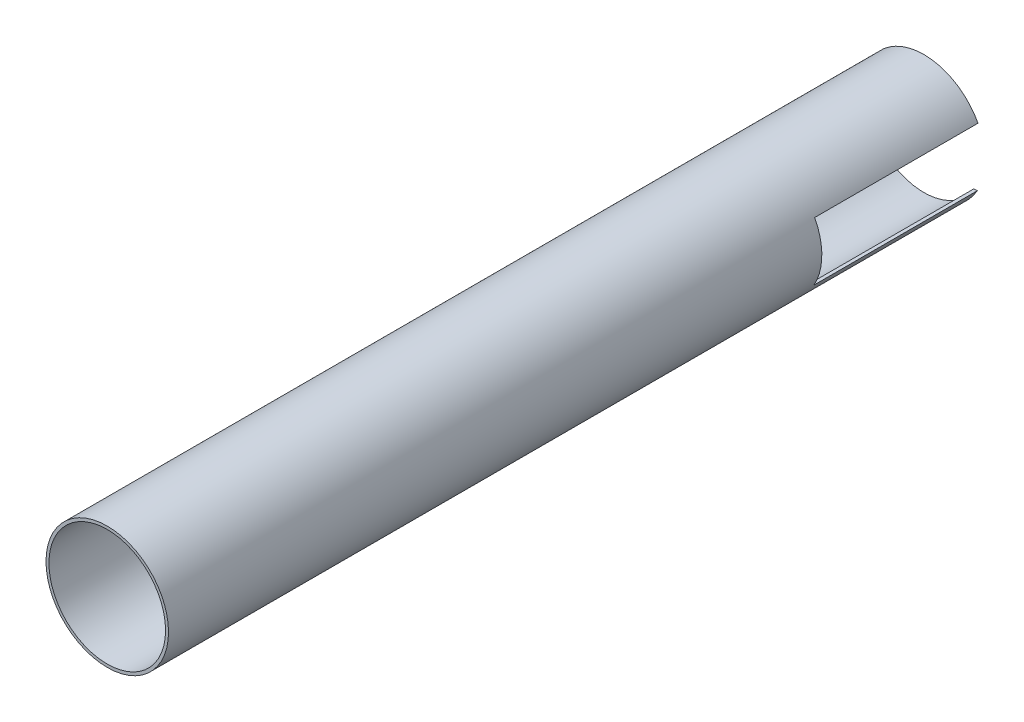
SolidWorks part; units mm, degrees
ref_plane "Front Plane" through (0, 0, 0) normal (0, 0, 1) x (1, 0, 0)
ref_plane "Top Plane" through (0, 0, 0) normal (0, 1, 0) x (1, 0, 0)
ref_plane "Right Plane" through (0, 0, 0) normal (1, 0, 0) x (0, 0, -1)
sketch "Sketch2" plane through (0, 0, 0) normal (0, 0, 1) x (1, 0, 0)
  circle A0 centre (0, 0) radius 37.5
  dimension "D1" = 75
extrude "Boss-Extrude1" add sketch "Sketch2" along normal blind 500
sketch "Sketch3" plane through (0, 0, 500) normal (0, 0, 1) x (1, 0, 0)
  circle A0 centre (0, 0) radius 35.7
extrude "Cut-Extrude1" cut sketch "Sketch3" against normal blind 500
sketch "Sketch4" plane through (0, 0, 0) normal (1, 0, 0) x (0, 0, -1)
  line L0 (0, 0) -> (0, 17.6195)
  line L1 (0, -37.5) -> (0, 37.5) construction
  line L2 (0, 17.6195) -> (0, -18.3805)
  line L4 (0, -18.3805) -> (-100, -18.3805)
  line L5 (0, -18.3805) -> (0, 17.6195)
  line L6 (0, 17.6195) -> (-100, 17.6195)
  line L7 (-100, -18.3805) -> (-100, 17.6195)
  line L8 (0, 17.6195) -> (-100, 17.6195)
  line L9 (0, 17.6195) -> (0, -18.3805)
  line L10 (0, -18.3805) -> (-100, -18.3805)
  line L11 (-100, 17.6195) -> (-100, -18.3805)
extrude "Cut-Extrude2" cut sketch "Sketch4" against normal mid plane 1000 contours L6 L7 L4 L2
